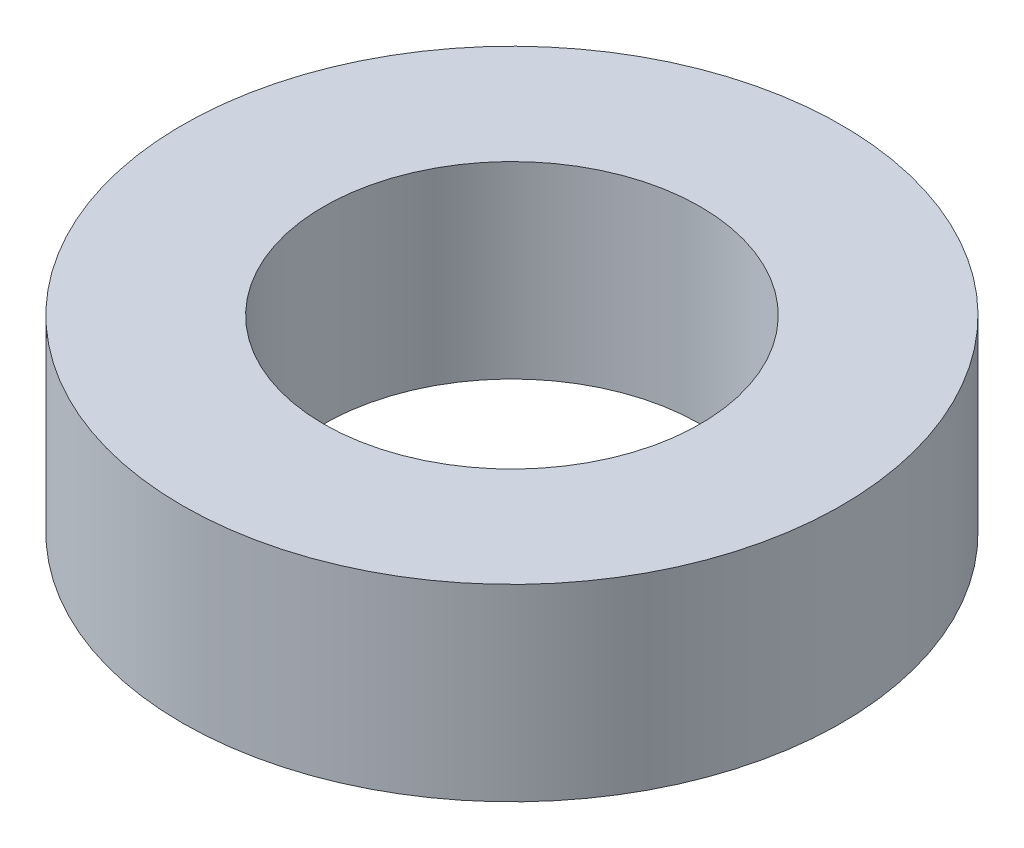
SolidWorks part; units mm, degrees
ref_plane "Front Plane" through (0, 0, 0) normal (0, 0, 1) x (1, 0, 0)
ref_plane "Top Plane" through (0, 0, 0) normal (0, 1, 0) x (1, 0, 0)
ref_plane "Right Plane" through (0, 0, 0) normal (1, 0, 0) x (0, 0, -1)
sketch "Sketch1" plane through (0, 0, 0) normal (0, 1, 0) x (1, 0, 0)
  circle A0 centre (0, 0) radius 1.5875
  circle A1 centre (0, 0) radius 2.7781
  dimension "D1" = 3.175
  dimension "D2" = 5.5562
extrude "Boss-Extrude1" add sketch "Sketch1" along normal blind 1.5875
